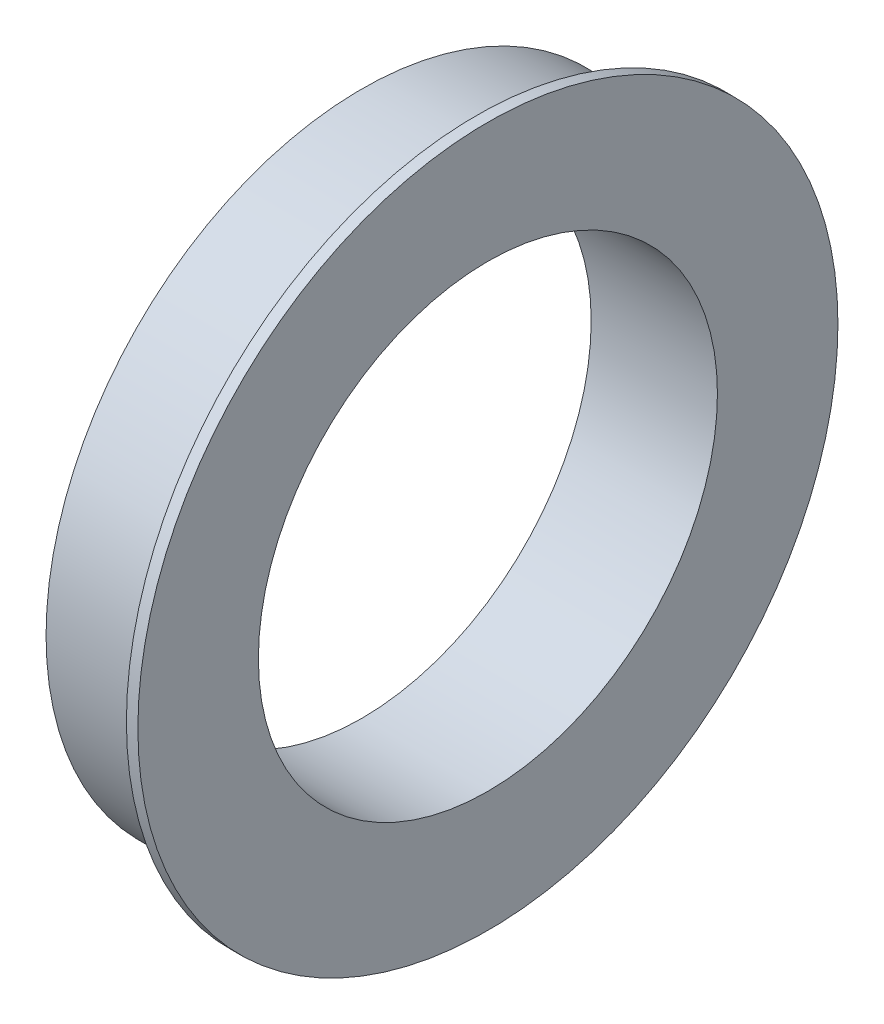
SolidWorks part; units mm, degrees
ref_plane "Front Plane" through (0, 0, 0) normal (0, 0, 1) x (1, 0, 0)
ref_plane "Top Plane" through (0, 0, 0) normal (0, 1, 0) x (1, 0, 0)
ref_plane "Right Plane" through (0, 0, 0) normal (1, 0, 0) x (0, 0, -1)
sketch "Sketch1" plane through (0, 0, 0) normal (0, 0, 1) x (1, 0, 0)
  line L0 (0, 0) -> (97.432, 0) construction
  line L1 (0, 40) -> (22, 40)
  line L2 (0, 40) -> (0, 55)
  line L3 (20, 61) -> (22, 61)
  line L4 (22, 40) -> (22, 61)
  line L5 (20, 61) -> (20, 55)
  line L6 (20, 55) -> (0, 55)
  dimension "D1" = 61
  dimension "D2" = 40
  dimension "D3" = 55
  dimension "D4" = 2
  dimension "D5" = 20
revolve "Revolve1" add sketch "Sketch1" angle 360 about L0
